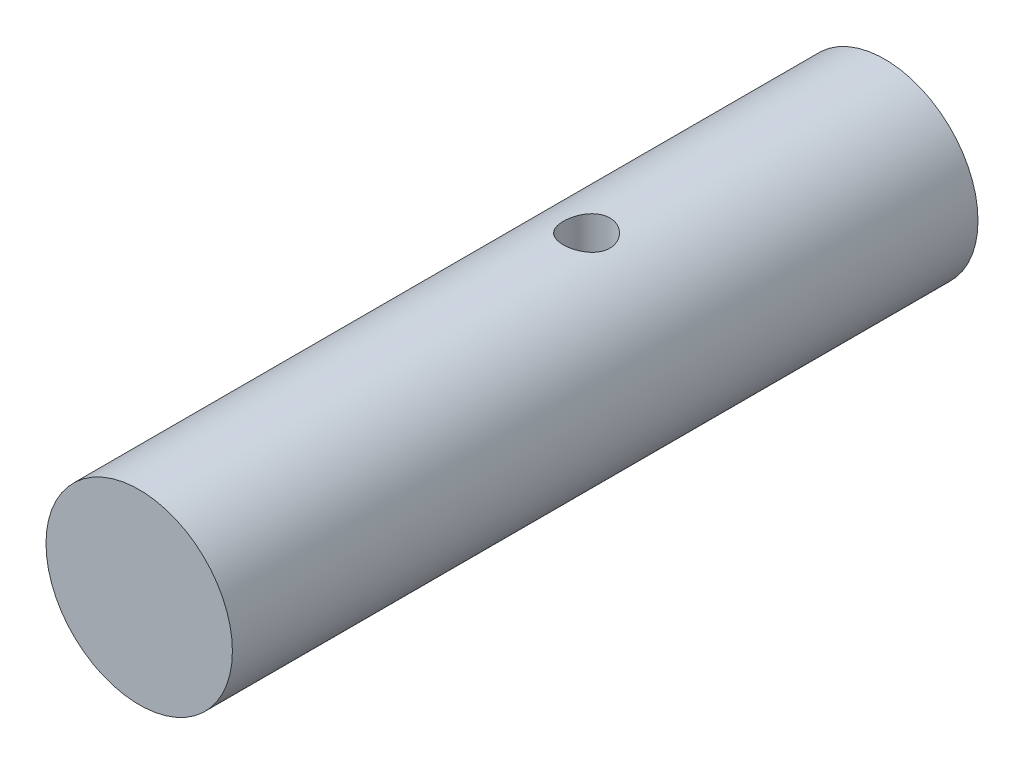
SolidWorks part; units mm, degrees
ref_plane "正面" through (0, 0, 0) normal (0, 0, 1) x (1, 0, 0)
ref_plane "平面" through (0, 0, 0) normal (0, 1, 0) x (1, 0, 0)
ref_plane "右側面" through (0, 0, 0) normal (1, 0, 0) x (0, 0, -1)
sketch "ｽｹｯﾁ2" plane through (0, 0, 0) normal (0, 0, 1) x (1, 0, 0)
  circle A0 centre (0, 0) radius 5
  dimension "D1" = 10
extrude "ﾎﾞｽ - 押し出し1" add sketch "ｽｹｯﾁ2" along normal blind 40
sketch "ｽｹｯﾁ3" plane through (0, 0, 0) normal (0, 1, 0) x (1, 0, 0)
  line L0 (0, 0) -> (0, -40) construction
  line L1 (-5, -40) -> (5, -40) construction
  line L2 (5, 0) -> (-5, 0) construction
  circle A0 centre (0, -16) radius 1.25
  dimension "D1" = 2.5
  dimension "D2" = 16
extrude "ｶｯﾄ - 押し出し1" cut sketch "ｽｹｯﾁ3" against normal through all both and the other way through all
